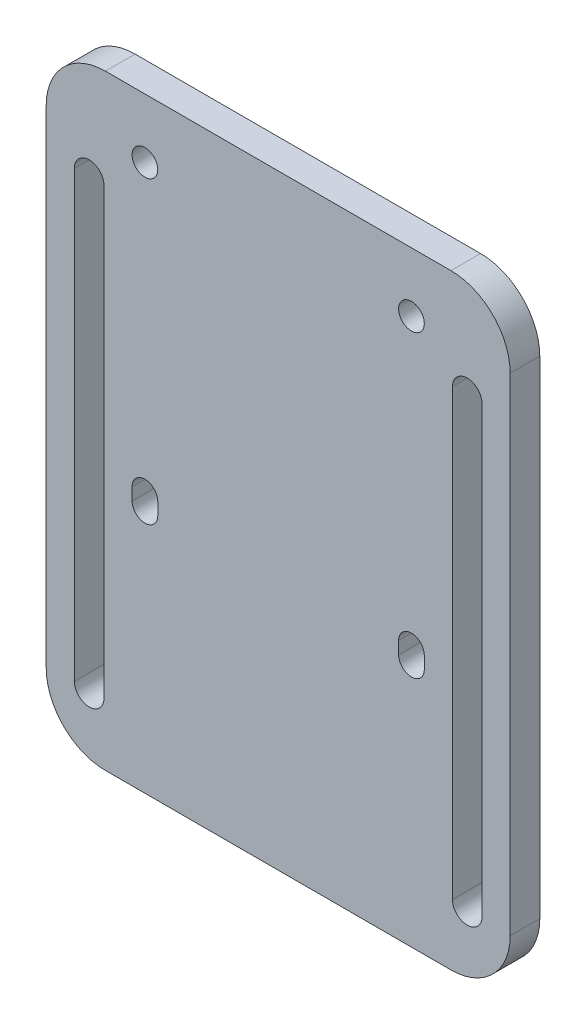
SolidWorks part; units mm, degrees
material "Acrylic (Medium-high impact)"
ref_plane "Спереди" through (0, 0, 0) normal (0, 0, 1) x (1, 0, 0)
ref_plane "Сверху" through (0, 0, 0) normal (0, 1, 0) x (1, 0, 0)
ref_plane "Справа" through (0, 0, 0) normal (1, 0, 0) x (0, 0, -1)
sketch "Model" plane through (0, 0, 0) normal (0, 0, 1) x (1, 0, 0)
  line L0 (0, 130.393) -> (0, -19.607) construction
  line L1 (38.3, 119.0065) -> (38.3, 3.8567) construction
  line L2 (39.6393, 110.7) -> (20.3566, 110.7) construction
  line L3 (27, 114.3973) -> (27, 106.7903) construction
  line L8 (27, 57.0366) -> (27, 46.0463) construction
  line L14 (-27, 114.3973) -> (-27, 106.7903) construction
  line L15 (-39.6393, 110.7) -> (-20.3566, 110.7) construction
  line L16 (-29.6, 50) -> (-29.6, 52.5)
  line L17 (-29.6, 52.5) -> (-29.6, 50)
  line L18 (-27, 57.0366) -> (-27, 46.0463) construction
  line L19 (-24.4, 52.5) -> (-24.4, 50)
  line L20 (-24.4, 50) -> (-24.4, 52.5)
  line L22 (-41.3, 12.5) -> (-41.3, 102.5)
  line L23 (-41.3, 102.5) -> (-41.3, 12.5)
  line L24 (-38.3, 119.0065) -> (-38.3, 3.8567) construction
  line L25 (-35.3, 102.5) -> (-35.3, 12.5)
  line L26 (-35.3, 12.5) -> (-35.3, 102.5)
  line L29 (-41.3, 12.5) -> (-35.3, 12.5) construction
  line L2974 (29.6, 52.5) -> (29.6, 50)
  line L2987 (24.4, 50) -> (24.4, 52.5)
  line L2994 (35.3, 12.5) -> (35.3, 102.5)
  line L3007 (41.3, 102.5) -> (41.3, 12.5)
  line L3504 (35, 0) -> (-35, 0)
  line L3511 (-47, 12) -> (-47, 110.7)
  line L3518 (-35, 122.7) -> (35, 122.7)
  line L3525 (47, 110.7) -> (47, 12)
  line L3777 (24.4, 52.5) -> (24.4, 50)
  line L3790 (29.6, 50) -> (29.6, 52.5)
  line L3887 (41.3, 12.5) -> (41.3, 102.5)
  line L3900 (35.3, 102.5) -> (35.3, 12.5)
  arc A0 (-47, 12) -> (-35, 0) centre (-35, 12) ccw
  arc A1 (35, 0) -> (47, 12) centre (35, 12) ccw
  arc A2 (47, 110.7) -> (35, 122.7) centre (35, 110.7) ccw
  arc A3 (-47, 110.7) -> (-35, 122.7) centre (-35, 110.7) cw
  circle A8 centre (27, 110.7) radius 2.6
  arc A9 (24.4, 52.5) -> (29.6, 52.5) centre (27, 52.5) cw
  arc A10 (24.4, 50) -> (29.6, 50) centre (27, 50) ccw
  arc A11 (35.3, 12.5) -> (41.3, 12.5) centre (38.3, 12.5) ccw
  arc A12 (35.3, 102.5) -> (41.3, 102.5) centre (38.3, 102.5) cw
  arc A17 (-35.3, 102.5) -> (-41.3, 102.5) centre (-38.3, 102.5) ccw
  circle A18 centre (-27, 110.7) radius 2.6
  arc A19 (-24.4, 50) -> (-29.6, 50) centre (-27, 50) cw
  arc A20 (-24.4, 52.5) -> (-29.6, 52.5) centre (-27, 52.5) ccw
  arc A22 (-35.3, 12.5) -> (-41.3, 12.5) centre (-38.3, 12.5) cw
  dimension "D1" = 12
  dimension "D17" = 5.2
  dimension "D22" = 2.6
  dimension "D23" = 2.6
  dimension "D26" = 90
  dimension "D2" = 70
  dimension "D3" = 122.7
  dimension "D4" = 38.3
  dimension "D5" = 58.2
  dimension "D6" = 11.3
  dimension "D19" = 11.3
  dimension "D20" = 2.5
  dimension "D21" = 5.2
  dimension "D24" = 50
  dimension "D25" = 6
  dimension "D27" = 12.5
extrude "Base" add sketch "Model" along normal blind 6
